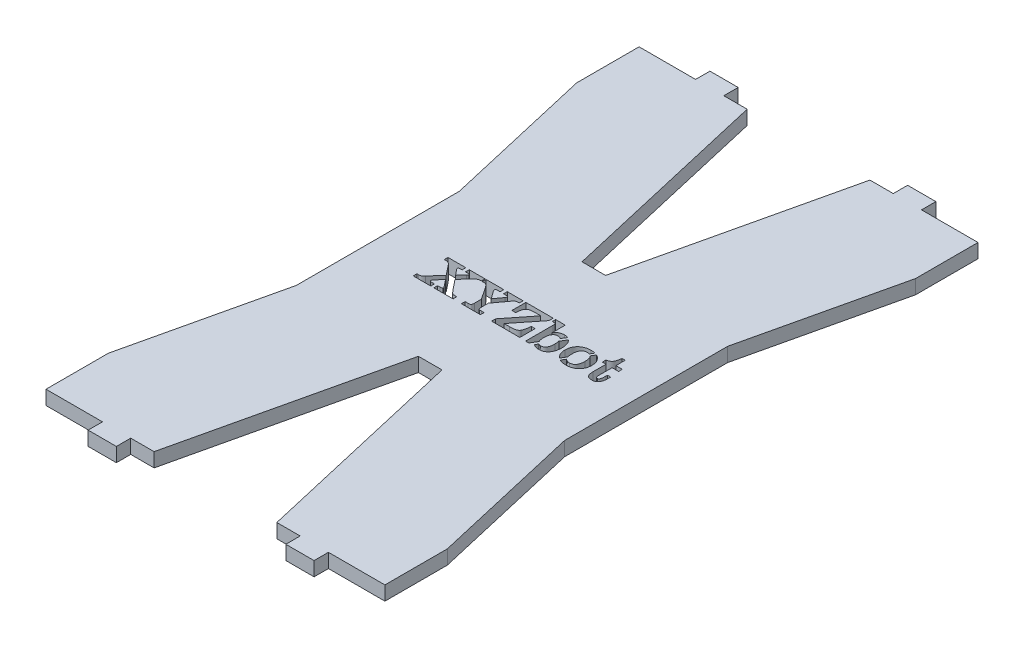
SolidWorks part; units mm, degrees
ref_plane "Front Plane" through (0, 0, 0) normal (0, 0, 1) x (1, 0, 0)
ref_plane "Top Plane" through (0, 0, 0) normal (0, 1, 0) x (1, 0, 0)
ref_plane "Right Plane" through (0, 0, 0) normal (1, 0, 0) x (0, 0, -1)
sketch "Sketch1" plane through (0, 0, 0) normal (0, 1, 0) x (1, 0, 0)
  line L1 (38.1, -66.675) -> (-38.1, -66.675)
  line L2 (38.1, -66.675) -> (38.1, 66.675)
  line L3 (38.1, 66.675) -> (-38.1, 66.675)
  line L4 (-38.1, -66.675) -> (-38.1, 66.675)
  line L5 (38.1, -66.675) -> (-38.1, 66.675) construction
  line L6 (38.1, 66.675) -> (-38.1, -66.675) construction
  point P0 (0, 0)
  dimension "D1" = 133.35
  dimension "D2" = 76.2
extrude "Boss-Extrude1" add sketch "Sketch1" along normal blind 3.175
sketch "Sketch2" plane through (0, 3.175, 0) normal (0, 1, 0) x (1, 0, 0)
  line L0 (-25.4, 66.675) -> (-25.4, 69.9008)
  line L1 (38.1, 66.675) -> (-38.1, 66.675) construction
  line L2 (-25.4, 69.9008) -> (-19.05, 69.9008)
  line L3 (-19.05, 69.9008) -> (-19.05, 66.675)
  line L4 (-19.05, 66.675) -> (-25.4, 66.675)
  line L5 (19.05, 66.675) -> (19.05, 69.9008)
  line L6 (19.05, 69.9008) -> (25.4, 69.9008)
  line L7 (25.4, 69.9008) -> (25.4, 66.675)
  line L8 (25.4, 66.675) -> (19.05, 66.675)
  line L9 (38.1, 66.675) -> (-38.1, 66.675) construction
  point P8 (0, 66.675)
  point P13 (0, 66.675)
  dimension "D1" = 3.2258
  dimension "D2" = 6.35
  dimension "D3" = 19.05
  dimension "D4" = 3.2258
  dimension "D5" = 6.35
  dimension "D6" = 19.05
extrude "Boss-Extrude2" add sketch "Sketch2" against normal blind 3.175
mirror "Mirror3" about plane through (0, 0, 0) normal (0, 0, 1) of "Boss-Extrude2"
sketch "Sketch4" plane through (0, 3.175, 0) normal (0, 1, 0) x (1, 0, 0)
  text T0 "XYZbot" font "Clarendon BT" height in points 28
extrude "Cut-Extrude1" cut sketch "Sketch4" against normal through all
sketch "Sketch5" plane through (0, 3.175, 0) normal (0, 1, 0) x (1, 0, 0)
  line L0 (7.6281, -2.6528) -> (10.5756, 2.1811)
  line L1 (10.5756, 2.1811) -> (11.1178, 1.8505)
  line L2 (11.1178, 1.8505) -> (7.7224, -3.7179)
  line L3 (7.7224, -3.7179) -> (7.1802, -3.3874)
  line L5 (7.1802, -3.3874) -> (7.6281, -2.6528)
  line L6 (17.0602, 2.836) -> (13.0817, -3.6887)
  line L7 (13.0817, -3.6887) -> (13.7179, -3.6887)
  line L8 (13.7179, -3.6887) -> (17.6952, 2.834)
  line L9 (17.6952, 2.834) -> (17.0602, 2.836)
  dimension "D1" = 0.635
  dimension "D2" = 0.635
extrude "Boss-Extrude4" add sketch "Sketch5" against normal blind 3.175
sketch "Sketch6" plane through (0, 3.175, 0) normal (0, 1, 0) x (1, 0, 0)
  line L0 (0, 66.675) -> (0, -66.675) construction
  line L1 (19.05, 66.675) -> (-19.05, 66.675) construction
  line L2 (-19.05, -66.675) -> (19.05, -66.675) construction
  line L3 (-38.1, 0) -> (38.1, 0) construction
  line L4 (-38.1, 66.675) -> (-38.1, -66.675) construction
  line L5 (38.1, -66.675) -> (38.1, 66.675) construction
  line L6 (-13.7977, 66.675) -> (-2.6513, 18.3948)
  line L7 (-2.6513, 18.3948) -> (0, 18.3948)
  line L8 (0, 18.3948) -> (0, 66.675)
  line L9 (0, 66.675) -> (-13.7977, 66.675)
  line L10 (-30.1749, 0) -> (-30.1749, 18.3193)
  line L11 (-30.1749, 18.3193) -> (-38.1, 52.6465)
  line L12 (-38.1, 52.6465) -> (-38.1, 0)
  line L13 (-38.1, 0) -> (-30.1749, 0)
  dimension "D1" = 77
extrude "Cut-Extrude2" cut sketch "Sketch6" against normal through all
mirror "Mirror4" about plane through (0, 0, 0) normal (1, 0, 0) of "Cut-Extrude2"
mirror "Mirror5" about plane through (0, 0, 0) normal (0, 0, 1) of "Mirror4", "Cut-Extrude2"
